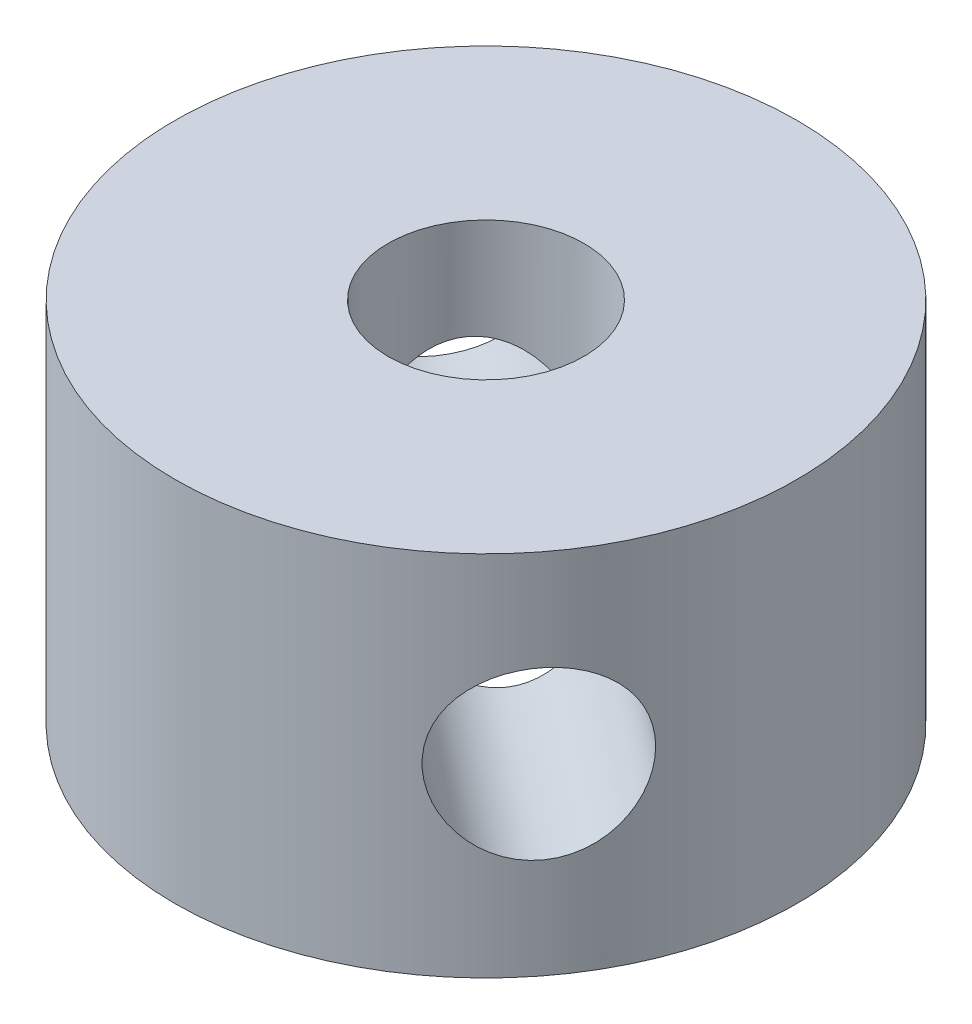
SolidWorks part; units mm, degrees
ref_plane "Front Plane" through (0, 0, 0) normal (0, 0, 1) x (1, 0, 0)
ref_plane "Top Plane" through (0, 0, 0) normal (0, 1, 0) x (1, 0, 0)
ref_plane "Right Plane" through (0, 0, 0) normal (1, 0, 0) x (0, 0, -1)
sketch "Sketch1" plane through (0, 0, 0) normal (0, 1, 0) x (1, 0, 0)
  circle A0 centre (0, 0) radius 4
  circle A1 centre (0, 0) radius 12.7
extrude "Boss-Extrude1" add sketch "Sketch1" along normal blind 15
hole_wizard "Ø6.8 (6.8) Diameter Hole1" positions "3DSketch1" profile "Sketch2" hole size "Ø6.8" standard "Ansi Metric"
sketch3d "3DSketch1"
  line L0 (0, 0, 0) -> (10.0297, 0, 7.7908)
  line L1 (10.0297, 0, 7.7908) -> (10.0297, 7.5, 7.7908)
  circle A0 centre (0, 0, 0) radius 12.7 construction
  point P0 (10.0297, 7.5, 7.7908)
  point P7 (0, 12.7, 0)
  dimension "D1" = 7.5
sketch "Sketch2" plane through (10.0297, 7.5, 7.7908) normal (0, 1, 0) x (0.6134, 0, -0.7897)
  line L0 (0, 0) -> (0, 302.0429)
  line L1 (0, 302.0429) -> (3.4, 300)
  line L2 (3.4, 300) -> (3.4, 0)
  line L5 (3.4, 0) -> (0, 0)
  line L10 (0, 302.0429) -> (-3.4, 300) construction
  line L11 (0, -6.35) -> (0, 107.95) construction
  dimension "Hole Dia." = 6.8
  dimension "Hole Depth" = 300
  dimension "Drill Angle" = 118
